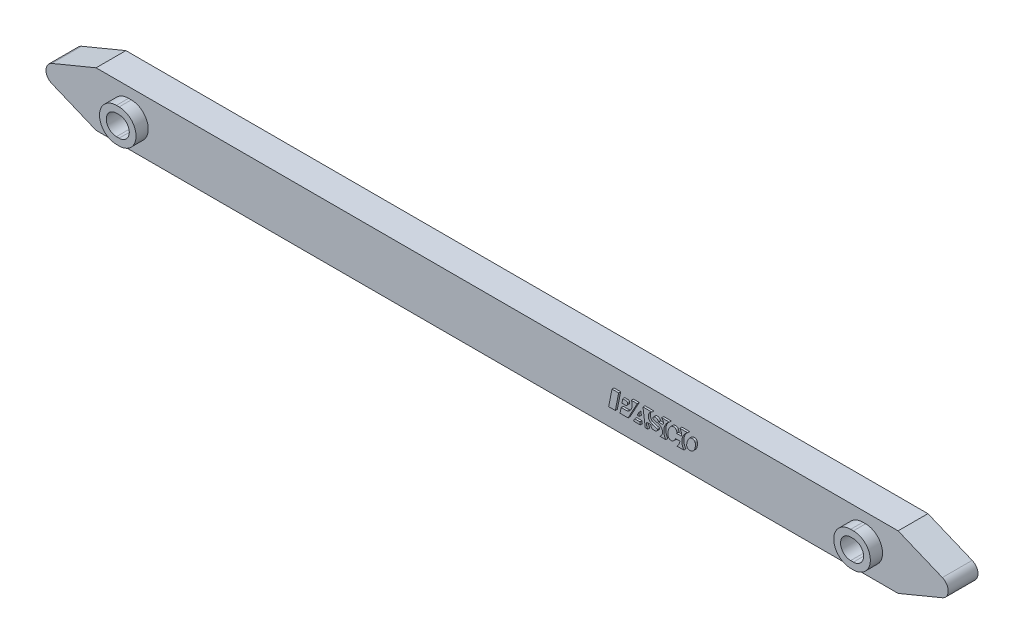
SolidWorks part; units mm, degrees
ref_plane "Front" through (0, 0, 0) normal (0, 0, 1) x (1, 0, 0)
ref_plane "Top" through (0, 0, 0) normal (0, 1, 0) x (1, 0, 0)
ref_plane "Right" through (0, 0, 0) normal (1, 0, 0) x (0, 0, -1)
sketch "Sketch1" plane through (0, 0, 0) normal (0, 0, 1) x (1, 0, 0)
  line L0 (-83.498, 1.6427) -> (-75.1995, 5.08)
  line L1 (0, 0) -> (-89.8026, 0) construction
  line L2 (-75.1995, 5.08) -> (75.1995, 5.08)
  line L3 (-75.1995, -5.08) -> (75.1995, -5.08)
  line L4 (-83.498, -1.6427) -> (-75.1995, -5.08)
  line L5 (0, 0) -> (89.8026, 0) construction
  line L6 (0, 0) -> (0, 29.7926) construction
  line L7 (83.498, -1.6427) -> (75.1995, -5.08)
  line L8 (83.498, 1.6427) -> (75.1995, 5.08)
  arc A0 (-83.498, 1.6427) -> (-83.498, -1.6427) centre (-82.8176, 0) ccw
  arc A1 (83.498, 1.6427) -> (83.498, -1.6427) centre (82.8176, 0) cw
  point P15 (0, -5.08)
  point P16 (0, 5.08)
extrude "Extrude1" add sketch "Sketch1" along normal mid plane 5.588
sketch "Sketch7" plane through (0, 0, -2.794) normal (0, 0, 1) x (1, 0, 0)
  line L0 (-69.1016, 0) -> (-68.5936, 0) construction
  line L1 (-69.1016, -1.905) -> (-68.5936, -1.905)
  line L2 (-69.1016, 1.905) -> (-68.5936, 1.905)
  line L3 (0, 0) -> (0, 10.2912) construction
  line L4 (69.1016, -1.905) -> (68.5936, -1.905)
  line L5 (69.1016, 1.905) -> (68.5936, 1.905)
  arc A0 (69.1016, -1.905) -> (69.1016, 1.905) centre (69.1016, 0) ccw
  arc A1 (-69.1016, -1.905) -> (-69.1016, 1.905) centre (-69.1016, 0) cw
  arc A2 (-68.5936, -1.905) -> (-68.5936, 1.905) centre (-68.5936, 0) ccw
  arc A3 (68.5936, -1.905) -> (68.5936, 1.905) centre (68.5936, 0) cw
  dimension "D4" = 68.5936
  dimension "D5" = 0.508
  dimension "D1" = 3.81
extrude "Cut-Extrude1" cut sketch "Sketch7" along normal through all
shell "Shell2" thickness 1.016
sketch "Sketch16" plane through (0, 0, 0) normal (0, 0, 1) x (1, 0, 0)
  line L0 (-68.5936, 1.905) -> (-69.1016, 1.905) construction
  line L1 (-69.1016, -1.905) -> (-68.5936, -1.905) construction
  line L2 (-68.5936, 1.905) -> (-69.1016, 1.905)
  line L3 (-69.1016, -1.905) -> (-68.5936, -1.905)
  line L4 (-68.5936, 3.175) -> (-69.1016, 3.175)
  line L5 (-69.1016, -3.175) -> (-68.5936, -3.175)
  line L6 (0, 0) -> (0, -31.1979) construction
  line L7 (69.1016, -3.175) -> (68.5936, -3.175)
  line L8 (68.5936, 3.175) -> (69.1016, 3.175)
  line L9 (69.1016, -1.905) -> (68.5936, -1.905)
  line L10 (68.5936, 1.905) -> (69.1016, 1.905)
  arc A0 (-69.1016, 1.905) -> (-69.1016, -1.905) centre (-69.1016, 0) ccw construction
  arc A1 (-68.5936, -1.905) -> (-68.5936, 1.905) centre (-68.5936, 0) ccw construction
  arc A2 (-69.1016, 1.905) -> (-69.1016, -1.905) centre (-69.1016, 0) ccw
  arc A3 (-68.5936, -1.905) -> (-68.5936, 1.905) centre (-68.5936, 0) ccw
  arc A4 (-69.1016, 3.175) -> (-69.1016, -3.175) centre (-69.1016, 0) ccw
  arc A5 (-68.5936, -3.175) -> (-68.5936, 3.175) centre (-68.5936, 0) ccw
  arc A6 (68.5936, -3.175) -> (68.5936, 3.175) centre (68.5936, 0) cw
  arc A7 (69.1016, 3.175) -> (69.1016, -3.175) centre (69.1016, 0) cw
  arc A8 (68.5936, -1.905) -> (68.5936, 1.905) centre (68.5936, 0) cw
  arc A9 (69.1016, 1.905) -> (69.1016, -1.905) centre (69.1016, 0) cw
  dimension "D1" = 1.27
extrude "Boss-Extrude1" add sketch "Sketch16" along normal blind 5.08
sketch "Sketch15" plane through (52.76, 8.5673, 2.794) normal (0, 0, 1) x (-1, 0, 0)
  line L0 (30.8336, 6.9093) -> (29.5859, 6.9093)
  line L1 (29.5859, 6.9093) -> (30.2098, 10.0807)
  line L2 (31.4575, 10.0807) -> (30.8336, 6.9093)
  line L3 (30.2098, 10.0807) -> (31.4575, 10.0807)
  line L4 (26.0981, 6.9093) -> (27.8182, 10.0807)
  line L5 (29.3259, 10.0807) -> (29.1214, 9.0409)
  line L6 (24.5948, 10.0807) -> (25.0248, 6.9093)
  line L7 (28.3121, 8.261) -> (28.9679, 8.261)
  line L8 (28.9679, 8.261) -> (28.8145, 7.4812)
  line L9 (28.8145, 7.4812) -> (28.2096, 7.4812)
  line L10 (27.9222, 7.7685) -> (27.9222, 7.8711)
  line L11 (27.1943, 6.9613) -> (27.2202, 6.9093)
  line L12 (27.2202, 6.9093) -> (26.0981, 6.9093)
  line L13 (29.1214, 9.0409) -> (28.0768, 9.0409)
  line L14 (25.7906, 8.1635) -> (25.7069, 8.7809)
  line L15 (25.7069, 8.7809) -> (26.1254, 8.7809)
  line L16 (26.1254, 8.7809) -> (25.7906, 8.1635)
  line L17 (23.3454, 6.9093) -> (23.451, 6.9613)
  line L18 (23.5123, 9.2465) -> (23.5123, 9.0409)
  line L19 (23.5123, 9.0409) -> (24.3348, 9.0409)
  line L20 (25.0248, 6.9093) -> (23.3454, 6.9093)
  line L21 (27.8182, 10.0807) -> (29.3259, 10.0807)
  line L22 (25.5306, 10.0807) -> (26.8304, 10.0807)
  line L23 (24.1269, 10.0807) -> (24.5948, 10.0807)
  line L24 (26.5766, 9.6128) -> (25.5941, 9.6128)
  line L25 (26.8304, 10.0807) -> (26.5766, 9.6128)
  line L26 (25.5941, 9.6128) -> (25.5306, 10.0807)
  line L27 (21.446, 6.9869) -> (21.5279, 6.9051)
  line L28 (21.5279, 6.9051) -> (20.0721, 6.9051)
  line L29 (22.1239, 8.1899) -> (22.96, 7.9808)
  line L30 (22.1005, 7.8936) -> (21.2687, 7.8936)
  line L31 (18.096, 6.9093) -> (16.6403, 6.9093)
  line L32 (18.096, 8.9889) -> (18.9279, 8.9889)
  line L33 (18.7199, 8.053) -> (17.7841, 8.053)
  line L34 (20.7475, 10.0807) -> (21.8393, 10.0807)
  line L35 (17.3681, 10.0807) -> (18.6679, 10.0807)
  line L36 (15.8073, 7.4274) -> (15.7153, 7.4274)
  arc A0 (23.6009, 8.7068) -> (22.4453, 9.0801) centre (21.8204, 5.1703) ccw
  arc A1 (23.2783, 9.5935) -> (22.5504, 9.5788) centre (22.9316, 8.7359) ccw
  arc A2 (23.1362, 7.7162) -> (22.96, 7.9808) centre (22.9027, 7.7517) ccw
  arc A3 (22.9171, 7.4486) -> (23.1362, 7.7162) centre (22.8011, 7.7671) ccw
  arc A4 (23.5123, 9.2465) -> (23.2783, 9.5935) centre (23.138, 9.2465) ccw
  arc A5 (24.3348, 9.0409) -> (24.1269, 10.0807) centre (23.0611, 9.3268) ccw
  arc A6 (27.9222, 7.7685) -> (28.2096, 7.4812) centre (28.2096, 7.7685) ccw
  arc A7 (28.3121, 8.261) -> (27.9222, 7.8711) centre (28.3121, 7.8711) ccw
  arc A8 (28.0768, 9.0409) -> (27.8619, 8.9892) centre (28.0768, 8.5684) ccw
  arc A9 (27.8619, 8.9892) -> (27.1943, 6.9613) centre (28.5518, 7.6382) ccw
  arc A10 (23.451, 6.9613) -> (23.7205, 8.6209) centre (22.9955, 7.8869) ccw
  arc A11 (23.7205, 8.6209) -> (23.6009, 8.7068) centre (23.3885, 8.2848) ccw
  arc A12 (15.8073, 7.4274) -> (16.41, 7.7365) centre (15.8073, 8.1696) ccw
  arc A13 (16.8317, 8.9559) -> (16.2492, 9.5825) centre (16.2311, 8.9816) ccw
  arc A14 (22.3592, 9.4048) -> (22.3136, 9.2187) centre (22.593, 9.2488) ccw
  arc A15 (20.0721, 6.9051) -> (20.7475, 10.0807) centre (18.8421, 8.8263) ccw
  arc A16 (21.8393, 10.0807) -> (21.8284, 8.3207) centre (22.4135, 9.1971) ccw
  arc A17 (16.6403, 6.9093) -> (17.3681, 10.0807) centre (15.4948, 8.8414) ccw
  arc A18 (18.6679, 10.0807) -> (18.096, 8.9889) centre (19.9383, 8.7195) ccw
  arc A19 (19.4623, 9.6506) -> (18.9279, 8.9889) centre (19.9383, 8.7195) ccw
  arc A20 (20.3337, 9.1838) -> (19.4623, 9.6506) centre (19.7333, 9.1098) ccw
  arc A21 (22.3136, 9.2187) -> (22.4453, 9.0801) centre (22.4702, 9.2356) ccw
  arc A22 (21.8284, 8.3207) -> (22.1239, 8.1899) centre (22.3531, 9.1066) ccw
  arc A23 (22.1005, 7.8936) -> (22.9171, 7.4486) centre (22.705, 8.0311) ccw
  arc A24 (21.2687, 7.8936) -> (21.446, 6.9869) centre (22.0312, 7.5721) ccw
  arc A25 (20.0104, 7.7216) -> (20.3337, 9.1838) centre (18.1068, 8.9095) ccw
  arc A26 (19.3406, 7.2565) -> (20.0104, 7.7216) centre (19.2447, 8.1094) ccw
  arc A27 (18.7199, 8.053) -> (19.3406, 7.2565) centre (19.2745, 7.8451) ccw
  arc A28 (17.7841, 8.053) -> (18.096, 6.9093) centre (19.2745, 7.8451) ccw
  arc A29 (16.41, 7.7365) -> (16.8317, 8.9559) centre (14.5786, 9.0526) ccw
  arc A30 (22.5504, 9.5788) -> (22.3592, 9.4048) centre (22.7231, 9.1968) ccw
  arc A31 (16.0048, 9.5557) -> (15.392, 9.0389) centre (16.2918, 8.5938) ccw
  arc A32 (15.2228, 7.8387) -> (15.7153, 7.4274) centre (15.7153, 7.928) ccw
  arc A33 (15.392, 9.0389) -> (15.2228, 7.8387) centre (17.1222, 8.1829) ccw
  arc A34 (16.2492, 9.5825) -> (16.0048, 9.5557) centre (16.2226, 8.6983) ccw
extrude "Boss-Extrude2" add sketch "Sketch15" along normal blind 0.381
equation "\"D1@Sketch1\" = 10/ sqr( 2 ) "
